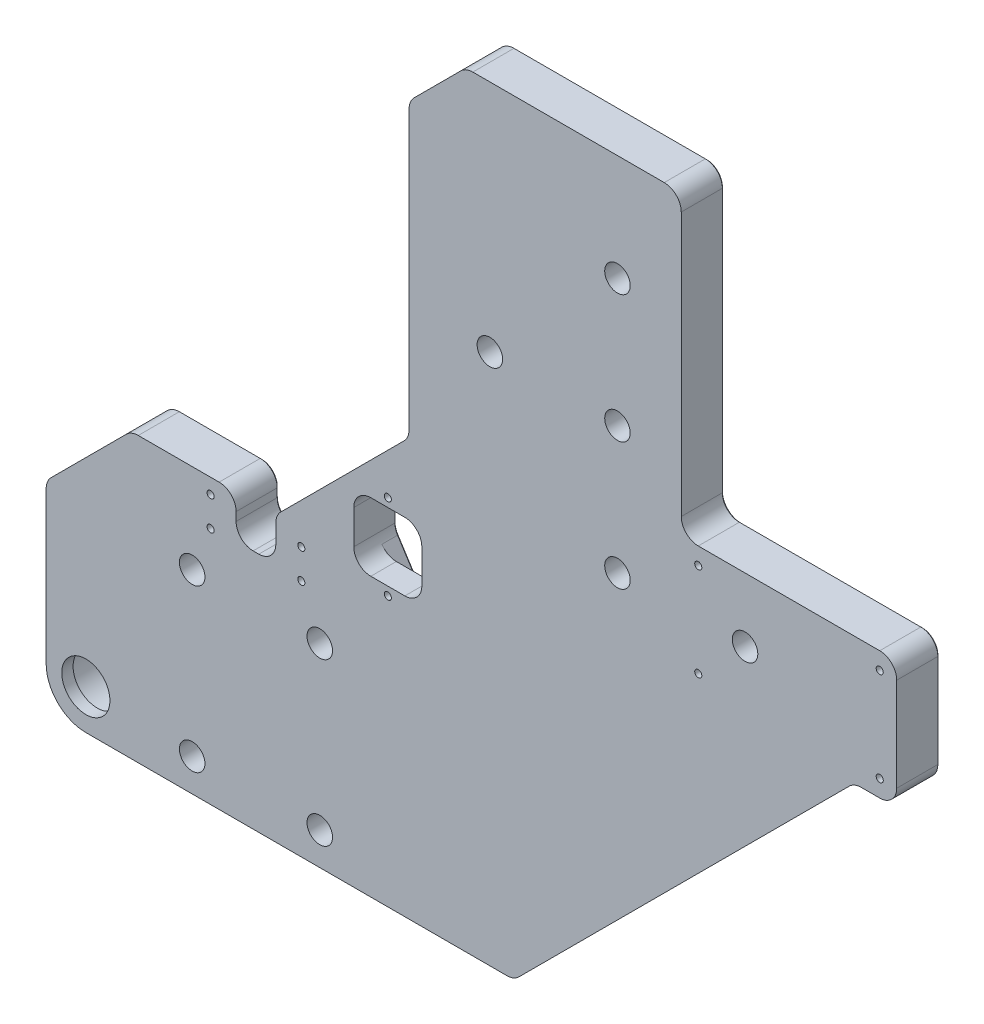
SolidWorks part; units mm, degrees
material "Alumina"
ref_plane "Plan de face" through (0, 0, 0) normal (0, 0, 1) x (1, 0, 0)
ref_plane "Plan de dessus" through (0, 0, 0) normal (0, 1, 0) x (1, 0, 0)
ref_plane "Plan de droite" through (0, 0, 0) normal (1, 0, 0) x (0, 0, -1)
sketch "Esquisse1" plane through (0, 0, 0) normal (0, 0, 1) x (1, 0, 0)
  line L0 (-21.0727, 123.2426) -> (54.9273, 123.2426)
  line L1 (54.9273, 123.2426) -> (54.9273, 18.2426)
  line L2 (54.9273, 18.2426) -> (130.9273, 18.2426)
  line L3 (130.9273, 18.2426) -> (130.9273, -26.7574)
  line L4 (-4.0727, -146.7574) -> (115.9273, -26.7574)
  line L5 (115.9273, -26.7574) -> (130.9273, -26.7574)
  line L6 (-4.0727, -146.7574) -> (-169.0727, -146.7574)
  line L7 (-169.0727, -146.7574) -> (-169.0727, -76.7574)
  line L8 (-21.0727, 123.2426) -> (-41.0727, 103.2426)
  line L11 (-41.0727, 0.2426) -> (-88.0727, -46.7574)
  line L13 (-169.0727, -76.7574) -> (-139.0727, -46.7574)
  line L14 (-41.0727, 103.2426) -> (-41.0727, 0.2426)
  line L16 (-88.0727, -46.7574) -> (-139.0727, -46.7574)
  circle A0 centre (-86.0562, -91.7574) radius 5.5 construction
  point P9 (-41.0727, 123.2426)
  point P15 (-41.0727, -46.7574)
  point P20 (-169.0727, -46.7574)
  dimension "D5" = 55
  dimension "D3" = 76
  dimension "D4" = 45
  dimension "D6" = 105
  dimension "D7" = 45
  dimension "D8" = 100
  dimension "D9" = 128
  dimension "D13" = 165
  dimension "D14" = 120
extrude "Boss.-Extru.1" add sketch "Esquisse1" along normal blind 15
hole_wizard "Chambrage pour vis à tête hexagonale M81" positions "Esquisse2" profile "Esquisse3" counterbore size "M8" standard "ISO" end condition through all
sketch "Esquisse2" plane through (0, 0, 0) normal (0, 0, -1) x (-1, 0, 0)
  line L2 (169.0727, -146.7574) -> (4.0727, -146.7574) construction
  line L3 (169.0727, -76.7574) -> (169.0727, -146.7574) construction
  line L18 (-54.9273, 18.2426) -> (-54.9273, 123.2426) construction
  line L19 (-54.9273, 123.2426) -> (21.0727, 123.2426) construction
  point P0 (72.5727, -78.2574)
  point P3 (117.5727, -78.2574)
  point P6 (72.5727, -135.2574)
  point P9 (117.5727, -135.2574)
  point P101 (-32.4273, 85.7426)
  point P103 (-32.4273, 40.7426)
  point P105 (-32.4273, -4.2574)
  point P107 (-77.4273, -4.2574)
  point P118 (12.5727, 40.7426)
  dimension "D1" = 57
  dimension "D2" = 45
  dimension "D3" = 11.5
  dimension "D4" = 51.5
  dimension "D5" = 22.5
  dimension "D6" = 45
  dimension "D7" = 45
  dimension "D8" = 45
  dimension "D9" = 37.5
  dimension "D10" = 45
sketch "Esquisse3" plane through (-72.5727, -78.2574, 0) normal (1, 0, 0) x (0, 1, 0)
  line L0 (0, 0) -> (0, 15)
  line L1 (0, 15) -> (4.5, 15)
  line L3 (4.5, 15) -> (4.5, 8.6)
  line L4 (4.5, 8.6) -> (7.5, 8.6)
  line L5 (7.5, 8.6) -> (7.5, 0)
  line L7 (7.5, 0) -> (0, 0)
  line L11 (0, -6.35) -> (0, 107.95) construction
  dimension "Diamètre du perçage jusqu'au prochain" = 9
  dimension "Profondeur du perçage jusqu'au prochain" = 15
  dimension "Diamètre du chambrage" = 15
  dimension "Profondeur du chambrage" = 8.6
hole_wizard "Tap Drill for M5 Tap1" positions "Sketch9" profile "Sketch10" hole size "M5" standard "ISO"
sketch "Sketch9" plane through (0, -146.7574, 0) normal (0, -1, 0) x (-1, 0, 0)
  line L0 (169.0727, 0) -> (4.0727, 0) construction
  line L3 (4.0727, -15) -> (4.0727, 0) construction
  point P0 (13.0727, -7.5)
  dimension "D1" = 7.5
  dimension "D2" = 9
sketch "Sketch10" plane through (-13.0727, -146.7574, 7.5) normal (1, 0, 0) x (0, 0, -1)
  line L0 (0, 0) -> (0, 14.2618)
  line L1 (0, 14.2618) -> (2.1, 13)
  line L2 (2.1, 13) -> (2.1, 0)
  line L5 (2.1, 0) -> (0, 0)
  line L10 (0, 14.2618) -> (-2.1, 13) construction
  line L11 (0, -6.35) -> (0, 107.95) construction
  dimension "Hole Dia." = 4.2
  dimension "Hole Depth" = 13
  dimension "Drill Angle" = 118
sketch "Sketch25" plane through (0, 0, 0) normal (0, 0, -1) x (-1, 0, 0)
  line L1 (88.0727, -46.7574) -> (102.0727, -46.7574)
  line L2 (88.0727, -46.7574) -> (88.0727, -61.7574)
  line L3 (88.0727, -61.7574) -> (102.0727, -61.7574)
  line L4 (102.0727, -46.7574) -> (102.0727, -61.7574)
  dimension "D1" = 14
  dimension "D2" = 15
extrude "Cut-Extrude6" cut sketch "Sketch25" against normal through all
fillet "Congé1" radius 6 15 edges at (54.9273, 18.2426, 7.5) (-41.0727, 103.2426, 7.5) (-41.0727, 0.2426, 7.5) (-169.0727, -76.7574, 7.5) (-139.0727, -46.7574, 7.5) (-21.0727, 123.2426, 7.5) (54.9273, 123.2426, 7.5) (130.9273, 18.2426, 7.5) (-4.0727, -146.7574, 7.5) (130.9273, -26.7574, 7.5) (115.9273, -26.7574, 7.5) (-102.0727, -61.7574, 7.5) (-88.0727, -61.7574, 7.5) (-102.0727, -46.7574, 7.5) (-88.0727, -46.7574, 7.5)
sketch "Sketch11" plane through (0, 0, 0) normal (0, 0, -1) x (-1, 0, 0)
  line L0 (169.0727, -79.2427) -> (169.0727, -146.7574) construction
  line L1 (169.0727, -146.7574) -> (6.558, -146.7574) construction
  circle A0 centre (155.0727, -132.7574) radius 8.5
  dimension "D1" = 17
  dimension "D2" = 14
  dimension "D3" = 14
extrude "Cut-Extrude1" cut sketch "Sketch11" against normal through all
sketch "Sketch12" plane through (0, 0, 0) normal (0, 0, -1) x (-1, 0, 0)
  circle A0 centre (155.0727, -132.7574) radius 11
  dimension "D1" = 22
extrude "Cut-Extrude2" cut sketch "Sketch12" against normal blind 11
sketch "Sketch13" plane through (0, 0, 0) normal (0, 0, -1) x (-1, 0, 0)
  line L1 (60.5727, -24.7574) -> (36.5727, -24.7574)
  line L2 (60.5727, -24.7574) -> (60.5727, -48.7574)
  line L3 (60.5727, -48.7574) -> (36.5727, -48.7574)
  line L4 (36.5727, -24.7574) -> (36.5727, -48.7574)
  line L5 (60.5727, -24.7574) -> (36.5727, -48.7574) construction
  line L6 (60.5727, -48.7574) -> (36.5727, -24.7574) construction
  line L8 (108.0727, -46.7574) -> (136.5874, -46.7574) construction
  line L9 (41.0727, 100.7573) -> (41.0727, 2.7279) construction
  point P0 (48.5727, -36.7574)
  dimension "D1" = 10
  dimension "D2" = 7.5
  dimension "D3" = 24
  dimension "D4" = 24
extrude "Cut-Extrude3" cut sketch "Sketch13" against normal through all
fillet "Fillet1" radius 6 4 edges at (-60.5727, -48.7574, 7.5) (-36.5727, -48.7574, 7.5) (-36.5727, -24.7574, 7.5) (-60.5727, -24.7574, 7.5)
sketch "Sketch14" plane through (0, 0, 0) normal (0, 0, -1) x (-1, 0, 0)
  line L11 (48.5727, -36.7574) -> (57.1396, -36.7574) construction
  line L14 (48.5727, -21.7574) -> (48.5727, -51.7574) construction
  line L15 (53.7941, -18.4142) -> (59.6257, -27.5221)
  line L16 (43.3513, -18.4142) -> (37.5197, -27.5221)
  line L17 (36.5727, -30.7574) -> (36.5727, -42.7574)
  line L18 (60.5727, -42.7574) -> (60.5727, -30.7574)
  line L20 (43.3513, -55.1006) -> (37.5197, -45.9927)
  line L21 (53.7941, -55.1006) -> (59.6257, -45.9927)
  arc A10 (53.7941, -18.4142) -> (43.3513, -18.4142) centre (48.5727, -21.7574) ccw
  arc A11 (43.3513, -55.1006) -> (53.7941, -55.1006) centre (48.5727, -51.7574) ccw
  arc A12 (36.5727, -42.7574) -> (37.5197, -45.9927) centre (42.5727, -42.7574) ccw
  arc A13 (59.6257, -45.9927) -> (60.5727, -42.7574) centre (54.5727, -42.7574) ccw
  arc A14 (37.5197, -27.5221) -> (36.5727, -30.7574) centre (42.5727, -30.7574) ccw
  arc A15 (60.5727, -30.7574) -> (59.6257, -27.5221) centre (54.5727, -30.7574) ccw
  point P5 (48.5727, -36.7574)
  dimension "D4" = 6.2
extrude "Cut-Extrude4" cut sketch "Sketch14" against normal blind 6
fillet "Fillet3" radius 14 1 edges at (-169.0727, -146.7574, 7.5)
hole_wizard "Tap Drill for M3 Tap1" positions "Sketch15" profile "Sketch16" hole size "M3" standard "ISO" end condition through all
sketch "Sketch15" plane through (0, 0, 6) normal (0, 0, -1) x (-1, 0, 0)
  point P1 (48.5727, -21.7574)
  point P4 (48.5727, -51.7574)
sketch "Sketch16" plane through (-48.5727, -21.7574, 6) normal (1, 0, 0) x (0, 1, 0)
  line L0 (0, 0) -> (0, 9)
  line L1 (0, 9) -> (1.25, 9)
  line L2 (1.25, 9) -> (1.25, 0)
  line L5 (1.25, 0) -> (0, 0)
  line L11 (0, -6.35) -> (0, 107.95) construction
  dimension "Thru Hole Dia." = 2.5
  dimension "Thru Hole Depth" = 9
chamfer "Chamfer1" distance 0.5 angle 45 54 edges at (-166.0727, -132.7574, 0) (-125.0727, -135.2574, 0) (-80.0727, -135.2574, 0) (-125.0727, -78.2574, 0) (-80.0727, -78.2574, 0) (-20.0727, 40.7426, 0) (69.9273, -4.2574, 0) (24.9273, 85.7426, 0) (24.9273, 40.7426, 0) (24.9273, -4.2574, 0) (130.9273, -4.2574, 0) (-80.8153, -146.7574, 0) (129.17, 16.4852, 0) (92.9273, 18.2426, 0) (-169.0727, -106, 0) (56.6847, 20, 0) (-168.616, -76.9466, 0) (54.9273, 70.7426, 0) (-154.0727, -61.7574, 0) (53.17, 121.4852, 0) (-138.8835, -47.2141, 0) (15.17, 123.2426, 0) (-122.33, -46.7574, 0) (-20.8835, 122.7859, 0) (-31.0727, 113.2426, 0) (-64.5727, -23.2574, 0) (-40.616, 103.0534, 0) (-41.5294, 0.4318, 0) (-41.0727, 51.7426, 0) (-36.8143, -44.4429, 0) (-36.5727, -36.7574, 0) (-36.8143, -29.0719, 0) (-60.3311, -44.4429, 0) (-60.5727, -36.7574, 0) (-60.3311, -29.0719, 0) (116.1165, -27.2141, 0) (121.67, -26.7574, 0) (55.9273, -86.7574, 0) (129.17, -25, 0) (-4.2619, -146.3007, 0) (-164.9722, -142.6569, 0) (-40.4355, -50.5467, 0) (-48.5727, -57.9574, 0) (-40.4355, -22.9682, 0) (-56.7099, -50.5467, 0) (-48.5727, -15.5574, 0) (-56.7099, -22.9682, 0) (-103.83, -48.5148, 0) (-102.0727, -54.2574, 0) (-100.3153, -60, 0) (-95.0727, -61.7574, 0) (-89.83, -60, 0) (-88.0727, -52.5, 0) (-87.616, -46.9466, 0)
hole_wizard "Tap Drill for M3 Tap2" positions "Sketch18" profile "Sketch19" hole size "M3" standard "ISO" end condition through all
sketch "Sketch18" plane through (0, 0, 0) normal (0, 0, -1) x (-1, 0, 0)
  point P0 (-124.9273, 12.2426)
  point P3 (-124.9273, -20.7574)
  point P6 (-60.9273, 12.2426)
  point P8 (-60.9273, -20.7574)
sketch "Sketch19" plane through (124.9273, 12.2426, 0) normal (1, 0, 0) x (0, 1, 0)
  line L0 (0, 0) -> (0, 15)
  line L1 (0, 15) -> (1.25, 15)
  line L2 (1.25, 15) -> (1.25, 0)
  line L5 (1.25, 0) -> (0, 0)
  line L11 (0, -6.35) -> (0, 107.95) construction
  dimension "Thru Hole Dia." = 2.5
  dimension "Thru Hole Depth" = 15
hole_wizard "Tap Drill for M3 Tap3" positions "Sketch22" profile "Sketch23" hole size "M3" standard "ISO" end condition through all
sketch "Sketch22" plane through (0, 0, 15) normal (0, 0, 1) x (1, 0, 0)
  line L1 (-108.0727, -46.7574) -> (-136.5874, -46.7574) construction
  circle A1 centre (-117.5727, -78.2574) radius 4.5 construction
  point P0 (-111.0727, -52.0574)
  point P2 (-111.0727, -62.4574)
  point P4 (-79.0727, -62.4574)
  point P6 (-79.0727, -52.0574)
  point P21 (0, 0)
  dimension "D3" = 6.5
  dimension "D1" = 32
  dimension "D2" = 10.4
  dimension "D4" = 5.3
sketch "Sketch23" plane through (-111.0727, -52.0574, 15) normal (1, 0, 0) x (0, -1, 0)
  line L0 (0, 0) -> (0, 15)
  line L1 (0, 15) -> (1.25, 15)
  line L2 (1.25, 15) -> (1.25, 0)
  line L5 (1.25, 0) -> (0, 0)
  line L11 (0, -6.35) -> (0, 107.95) construction
  dimension "Thru Hole Dia." = 2.5
  dimension "Thru Hole Depth" = 15
